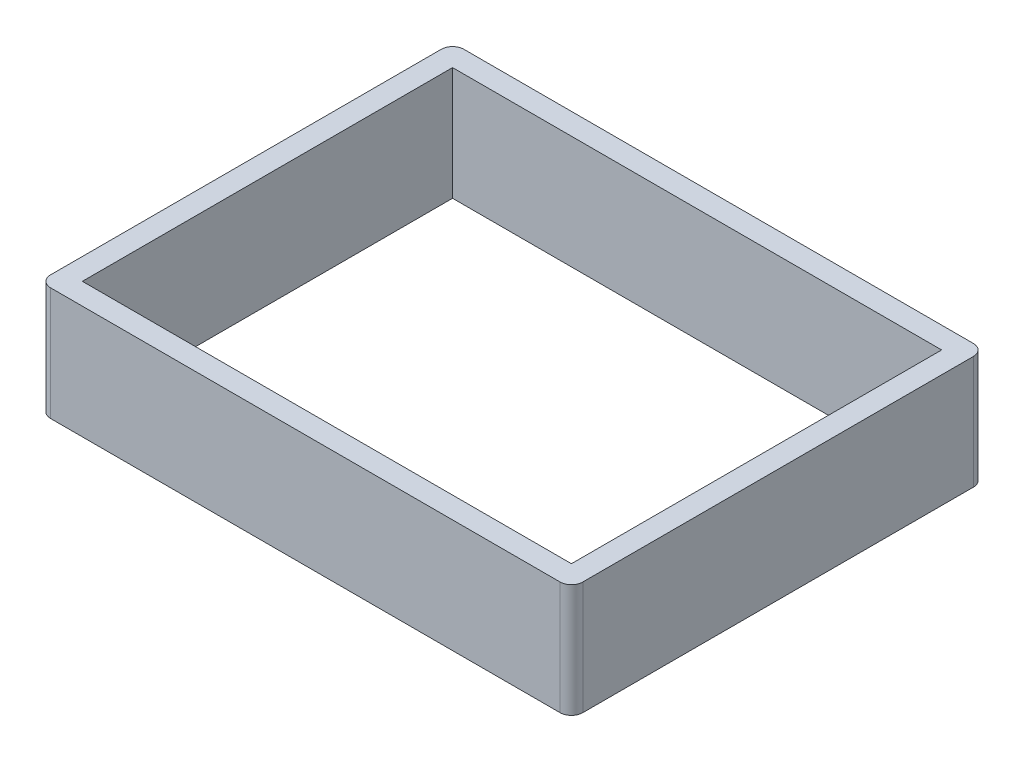
SolidWorks part; units mm, degrees
ref_plane "Front Plane" through (0, 0, 0) normal (0, 0, 1) x (1, 0, 0)
ref_plane "Top Plane" through (0, 0, 0) normal (0, 1, 0) x (1, 0, 0)
ref_plane "Right Plane" through (0, 0, 0) normal (1, 0, 0) x (0, 0, -1)
sketch "Sketch2" plane through (0, 0, 0) normal (0, 1, 0) x (1, 0, 0)
  line L1 (0, 0) -> (119.38, 0)
  line L2 (0, 0) -> (0, 92.71)
  line L3 (0, 92.71) -> (119.38, 92.71)
  line L4 (119.38, 0) -> (119.38, 92.71)
  line L5 (4.826, 87.884) -> (114.554, 87.884)
  line L6 (4.826, 87.884) -> (4.826, 4.826)
  line L7 (4.826, 4.826) -> (114.554, 4.826)
  line L8 (114.554, 87.884) -> (114.554, 4.826)
  point P9 (0, 0)
  dimension "D1" = 119.38
  dimension "D2" = 92.71
  dimension "D3" = 4.826
  dimension "D4" = 4.826
  dimension "D5" = 4.826
  dimension "D6" = 4.826
extrude "Boss-Extrude1" add sketch "Sketch2" along normal blind 25.4
fillet "Fillet1" radius 2.54 4 edges at (119.38, 12.7, 0) (0, 12.7, 0) (119.38, 12.7, -92.71) (0, 12.7, -92.71)
